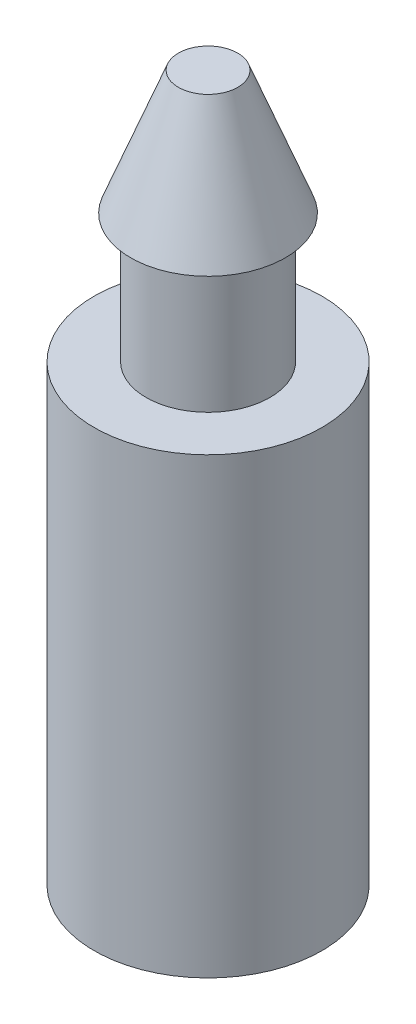
SolidWorks part; units mm, degrees
other "Markup1"
sketch "Sketch2" plane through (-1.1684, 7.239, 1.1684) normal (-0.4974, 0.5557, 0.6662) x (0.8627, 0.3979, 0.3122)
material "Brass"
ref_plane "Front Plane" through (0, 0, 0) normal (0, 0, 1) x (1, 0, 0)
ref_plane "Top Plane" through (0, 0, 0) normal (0, 1, 0) x (1, 0, 0)
ref_plane "Right Plane" through (0, 0, 0) normal (1, 0, 0) x (0, 0, -1)
sketch "Sketch1" plane through (0, 0, 0) normal (0, 0, 1) x (1, 0, 0)
  line L0 (0, 0) -> (0, 8.2444) construction
  line L1 (0, 0) -> (0, 7.239)
  line L3 (0.635, 5.969) -> (0.635, 4.6482)
  line L4 (0.635, 4.6482) -> (1.1684, 4.6482)
  line L5 (1.1684, 4.6482) -> (1.1684, 0)
  line L6 (1.1684, 0) -> (0, 0)
  line L8 (0, 7.239) -> (0.3044, 7.239)
  line L9 (0.635, 5.969) -> (0.7937, 5.969)
  line L10 (0.7937, 5.969) -> (0.3044, 7.239)
  dimension "D1" = 7.239
  dimension "D2" = 0.635
  dimension "D3" = 1.1684
  dimension "D4" = 4.6482
  dimension "D5" = 1.3208
  dimension "D6" = 0.7937
revolve "Revolve1" add sketch "Sketch1" angle 360 about L0
